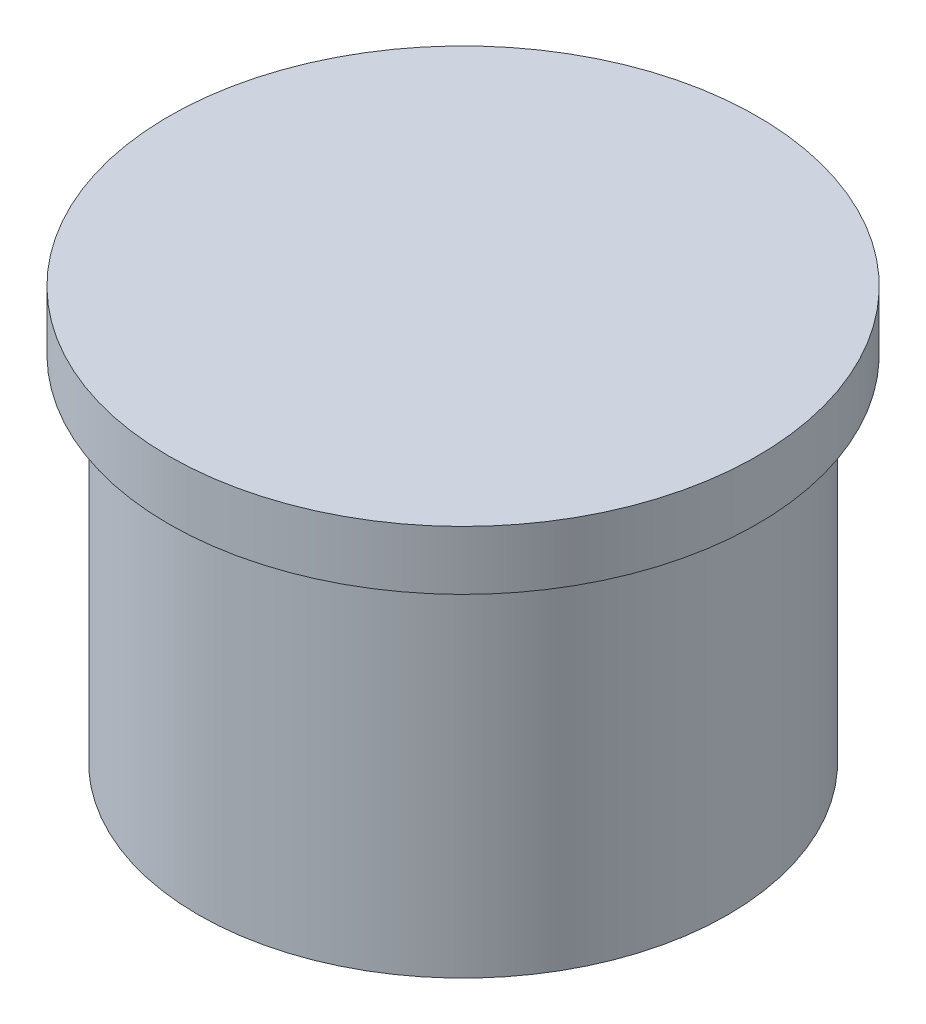
SolidWorks part; units mm, degrees
ref_plane "Front Plane" through (0, 0, 0) normal (0, 0, 1) x (1, 0, 0)
ref_plane "Top Plane" through (0, 0, 0) normal (0, 1, 0) x (1, 0, 0)
ref_plane "Right Plane" through (0, 0, 0) normal (1, 0, 0) x (0, 0, -1)
sketch "Sketch1" plane through (0, 0, 0) normal (0, 1, 0) x (1, 0, 0)
  circle A0 centre (0, 0) radius 2.25
extrude "Boss-Extrude1" add sketch "Sketch1" along normal blind 3
sketch "Sketch2" plane through (0, 3, 0) normal (0, 1, 0) x (1, 0, 0)
  circle A0 centre (0, 0) radius 2.5
extrude "Boss-Extrude2" add sketch "Sketch2" along normal blind 0.5
